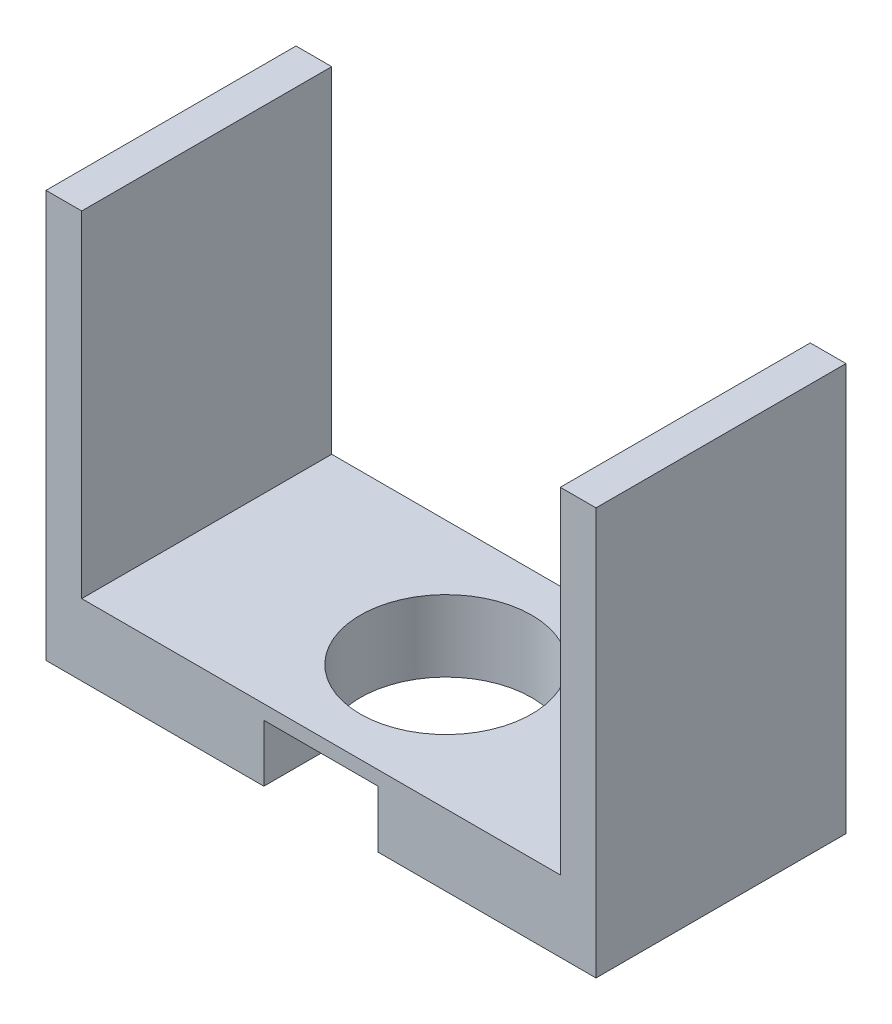
SolidWorks part; units mm, degrees
ref_plane "Plan de face" through (0, 0, 0) normal (0, 0, 1) x (1, 0, 0)
ref_plane "Plan de dessus" through (0, 0, 0) normal (0, 1, 0) x (1, 0, 0)
ref_plane "Plan de droite" through (0, 0, 0) normal (1, 0, 0) x (0, 0, -1)
sketch "Esquisse1" plane through (0, 0, 0) normal (0, 0, 1) x (1, 0, 0)
  line L0 (72, -57) -> (72, 0)
  line L1 (0, 0) -> (0, -47)
  line L2 (-5, -57) -> (72, -57)
  line L3 (-5, -57) -> (-5, 0)
  line L4 (33.5, 0) -> (33.5, 19.6794) construction
  line L5 (0, -47) -> (67, -47)
  line L6 (67, 0) -> (67, -47)
  line L7 (0, -57) -> (84.4789, -57) construction
  line L8 (0, -47) -> (84.4789, -47) construction
  line L9 (-5, 0) -> (0, 0)
  line L10 (67, 0) -> (72, 0)
extrude "Extrusion1" add sketch "Esquisse1" along normal blind 35
sketch "Esquisse2" plane through (0, -57, 0) normal (0, -1, 0) x (1, 0, 0)
  line L0 (-5, 35) -> (72, 0) construction
  circle A0 centre (33.5, 17.5) radius 12
extrude "Extrusion2" cut sketch "Esquisse2" against normal through all
sketch "Esquisse3" plane through (0, -57, 0) normal (0, -1, 0) x (1, 0, 0)
  line L0 (33.5, 17.5) -> (33.5, 29.5) construction
  line L1 (41.5, 26.4443) -> (41.5, 35)
  line L2 (25.5, 26.4443) -> (25.5, 35)
  line L3 (-5, 35) -> (72, 35) construction
  line L4 (25.5, 35) -> (41.5, 35)
  circle A0 centre (33.5, 17.5) radius 12 construction
  arc A1 (41.5, 26.4443) -> (25.5, 26.4443) centre (33.5, 17.5) ccw
extrude "Extrusion3" cut sketch "Esquisse3" against normal blind 8
